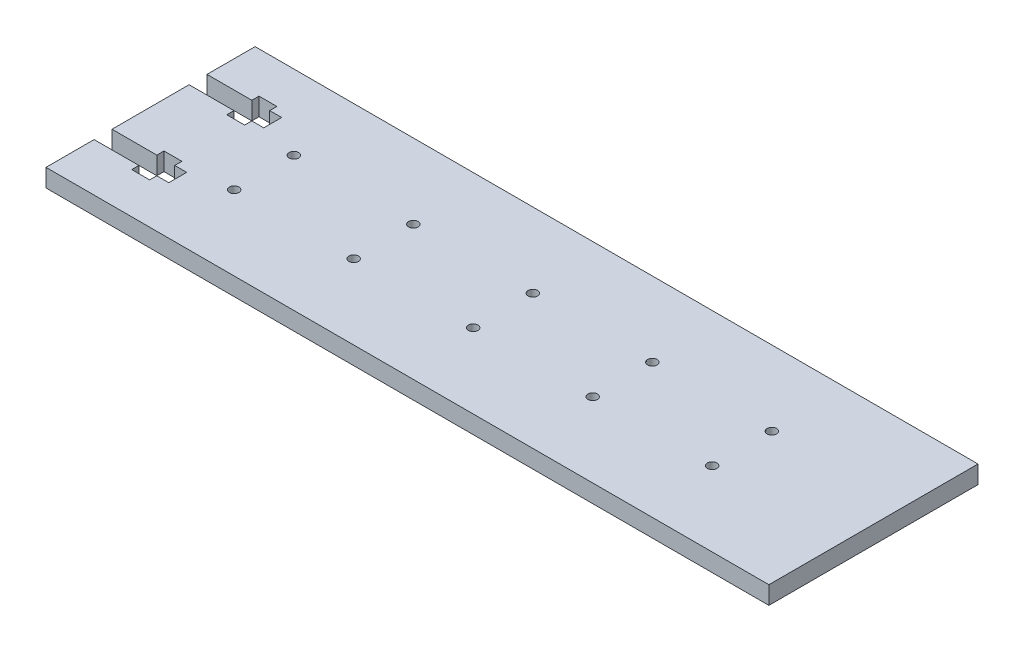
SolidWorks part; units mm, degrees
ref_plane "Front Plane" through (0, 0, 0) normal (0, 0, 1) x (1, 0, 0)
ref_plane "Top Plane" through (0, 0, 0) normal (0, 1, 0) x (1, 0, 0)
ref_plane "Right Plane" through (0, 0, 0) normal (1, 0, 0) x (0, 0, -1)
sketch "Sketch1" plane through (0, 0, 0) normal (0, 1, 0) x (1, 0, 0)
  line L1 (-121, -35) -> (121, -35)
  line L2 (-121, -35) -> (-121, 35)
  line L3 (-121, 35) -> (121, 35)
  line L4 (121, -35) -> (121, 35)
  line L5 (-121, -35) -> (121, 35) construction
  line L6 (-121, 35) -> (121, -35) construction
  circle A0 centre (77, -10) radius 1.6 construction
  circle A1 centre (77, 10) radius 1.6 construction
  circle A2 centre (37, -10) radius 1.6 construction
  circle A3 centre (37, 10) radius 1.6 construction
  circle A4 centre (-3, -10) radius 1.6 construction
  circle A5 centre (-3, 10) radius 1.6 construction
  circle A6 centre (-43, -10) radius 1.6 construction
  circle A7 centre (-43, 10) radius 1.6 construction
  circle A8 centre (-83, -10) radius 1.6 construction
  circle A9 centre (-83, 10) radius 1.6 construction
  circle A10 centre (77, -10) radius 1.6
  circle A11 centre (77, 10) radius 1.6
  circle A12 centre (37, -10) radius 1.6
  circle A13 centre (37, 10) radius 1.6
  circle A14 centre (-3, -10) radius 1.6
  circle A15 centre (-3, 10) radius 1.6
  circle A16 centre (-43, -10) radius 1.6
  circle A17 centre (-43, 10) radius 1.6
  circle A18 centre (-83, -10) radius 1.6
  circle A19 centre (-83, 10) radius 1.6
  point P0 (0, 0)
  dimension "D1" = 242
  dimension "D2" = 70
extrude "Boss-Extrude1" add sketch "Sketch1" along normal blind 6
sketch "Sketch3" plane through (0, 6, 0) normal (0, 1, 0) x (1, 0, 0)
  line L0 (-121, 0) -> (-96, 0) construction
  line L1 (-121, 35) -> (-121, -35) construction
  line L2 (-121, 15.9) -> (-96, 15.9) construction
  line L7 (-121, 12.9) -> (-106, 12.9)
  line L8 (-121, 18.9) -> (-106, 18.9)
  line L9 (-121, 12.9) -> (-121, 18.9)
  line L10 (-96, 12.9) -> (-96, 18.9)
  line L18 (-106, 10.5) -> (-100, 10.5)
  line L19 (-106, 10.5) -> (-106, 12.9)
  line L20 (-106, 21.3) -> (-100, 21.3)
  line L21 (-100, 10.5) -> (-100, 12.9)
  line L22 (-106, 10.5) -> (-100, 21.3) construction
  line L23 (-106, 21.3) -> (-100, 10.5) construction
  line L29 (-100, 18.9) -> (-100, 21.3)
  line L30 (-100, 18.9) -> (-96, 18.9)
  line L31 (-121, 18.9) -> (-96, 18.9) construction
  line L32 (-100, 12.9) -> (-96, 12.9)
  line L33 (-121, 12.9) -> (-96, 12.9) construction
  line L34 (-106, 18.9) -> (-106, 21.3)
  line L35 (-106, -21.3) -> (-100, -10.5) construction
  line L36 (-106, -10.5) -> (-100, -21.3) construction
  line L37 (-121, -15.9) -> (-96, -15.9) construction
  line L38 (-106, -18.9) -> (-106, -21.3)
  line L39 (-100, -12.9) -> (-96, -12.9)
  line L40 (-100, -18.9) -> (-96, -18.9)
  line L41 (-100, -18.9) -> (-100, -21.3)
  line L42 (-100, -10.5) -> (-100, -12.9)
  line L43 (-106, -21.3) -> (-100, -21.3)
  line L44 (-106, -10.5) -> (-106, -12.9)
  line L45 (-106, -10.5) -> (-100, -10.5)
  line L46 (-96, -12.9) -> (-96, -18.9)
  line L47 (-121, -12.9) -> (-121, -18.9)
  line L48 (-121, -18.9) -> (-106, -18.9)
  line L49 (-121, -12.9) -> (-106, -12.9)
  point P11 (-103, 15.9)
  point P47 (-103, -15.9)
  dimension "D3" = 15
  dimension "D4" = 15.9
  dimension "D7" = 25
  dimension "D1" = 10.8
  dimension "D2" = 6
  dimension "D5" = 3
  dimension "D6" = 3
extrude "Cut-Extrude2" cut sketch "Sketch3" against normal through all
